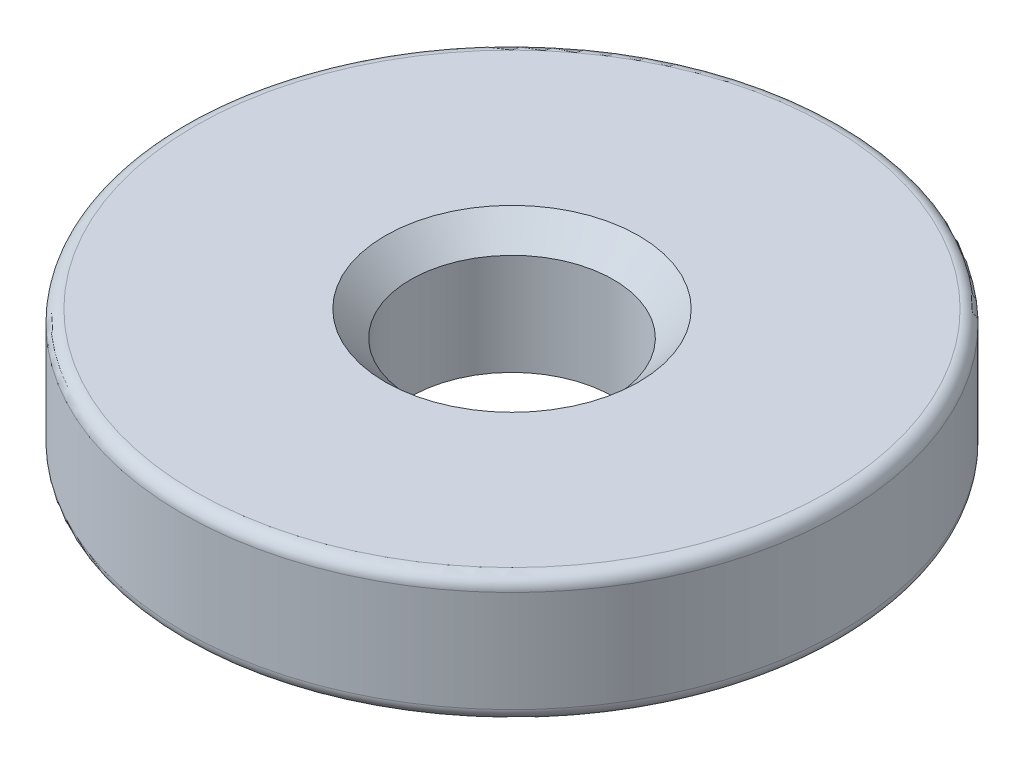
SolidWorks part; units mm, degrees
ref_plane "Front Plane" through (0, 0, 0) normal (0, 0, 1) x (1, 0, 0)
ref_plane "Top Plane" through (0, 0, 0) normal (0, 1, 0) x (1, 0, 0)
ref_plane "Right Plane" through (0, 0, 0) normal (1, 0, 0) x (0, 0, -1)
sketch "Sketch1" plane through (0, 0, 0) normal (0, 1, 0) x (1, 0, 0)
  circle A0 centre (0, 0) radius 13
  circle A1 centre (0, 0) radius 4
  dimension "D1" = 26
  dimension "D2" = 8
extrude "Boss-Extrude1" add sketch "Sketch1" along normal blind 5
chamfer "Chamfer1" distance 1 angle 45 1 edges at (0, 5, 4)
fillet "Fillet1" radius 0.5 2 edges at (0, 0, 13) (0, 5, 13)
